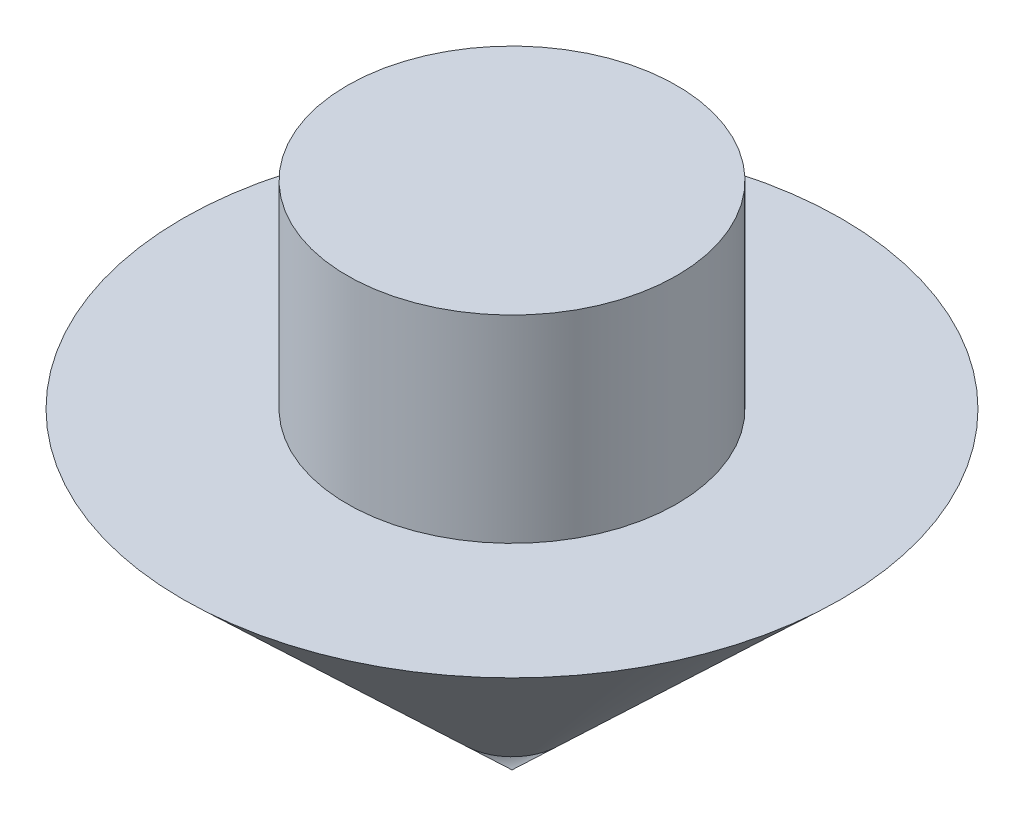
SolidWorks part; units mm, degrees
material "3003 Alloy"
ref_plane "Front Plane" through (0, 0, 0) normal (0, 0, 1) x (1, 0, 0)
ref_plane "Top Plane" through (0, 0, 0) normal (0, 1, 0) x (1, 0, 0)
ref_plane "Right Plane" through (0, 0, 0) normal (1, 0, 0) x (0, 0, -1)
sketch "Sketch1" plane through (0, 0, 0) normal (0, 0, 1) x (1, 0, 0)
  line L0 (0, 0) -> (10, 9.4896)
  line L1 (10, 9.4896) -> (-10, 9.4896)
  line L2 (-10, 9.4896) -> (0, 0)
  line L3 (0, 0) -> (0, 9.4896)
  dimension "D1" = 20
  dimension "D2" = 46.5
revolve "Revolve1" add sketch "Sketch1" angle 360 about L3
ref_axis "Axis1" through (0, 0, 0) along (0, 1, 0)
sketch "Sketch2" plane through (0, 0, 0) normal (0, 0, 1) x (1, 0, 0)
  line L0 (10, 9.4896) -> (-10, 9.4896) construction
  line L1 (0, 9.4896) -> (5, 9.4896)
  line L2 (0, 9.4896) -> (0, 15.4896)
  line L3 (0, 15.4896) -> (5, 15.4896)
  line L4 (5, 9.4896) -> (5, 15.4896)
  dimension "D1" = 6
  dimension "D2" = 5
revolve "Revolve2" add sketch "Sketch2" angle 360 about axis through (0, 0, 0) along (0, 1, 0)
